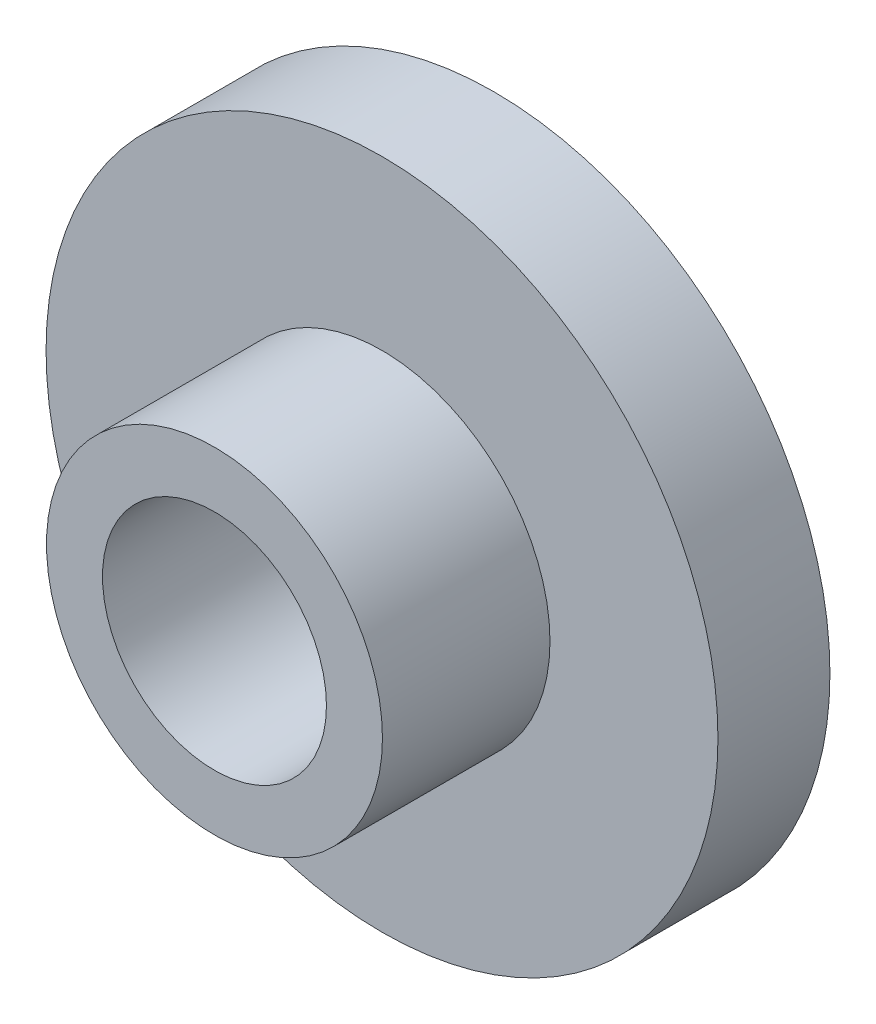
SolidWorks part; units mm, degrees
ref_plane "Front Plane" through (0, 0, 0) normal (0, 0, 1) x (1, 0, 0)
ref_plane "Top Plane" through (0, 0, 0) normal (0, 1, 0) x (1, 0, 0)
ref_plane "Right Plane" through (0, 0, 0) normal (1, 0, 0) x (0, 0, -1)
sketch "Sketch1" plane through (0, 0, 0) normal (0, 0, 1) x (1, 0, 0)
  circle A0 centre (0, 0) radius 9.525
extrude "Boss-Extrude1" add sketch "Sketch1" along normal blind 3.175
sketch "Sketch2" plane through (0, 0, 3.175) normal (0, 0, 1) x (1, 0, 0)
  circle A0 centre (0, 0) radius 4.7625
extrude "Boss-Extrude2" add sketch "Sketch2" along normal blind 4.7498
sketch "Sketch3" plane through (0, 0, 7.9248) normal (0, 0, 1) x (1, 0, 0)
  circle A0 centre (0, 0) radius 3.175
extrude "Cut-Extrude1" cut sketch "Sketch3" against normal blind 7.9756
